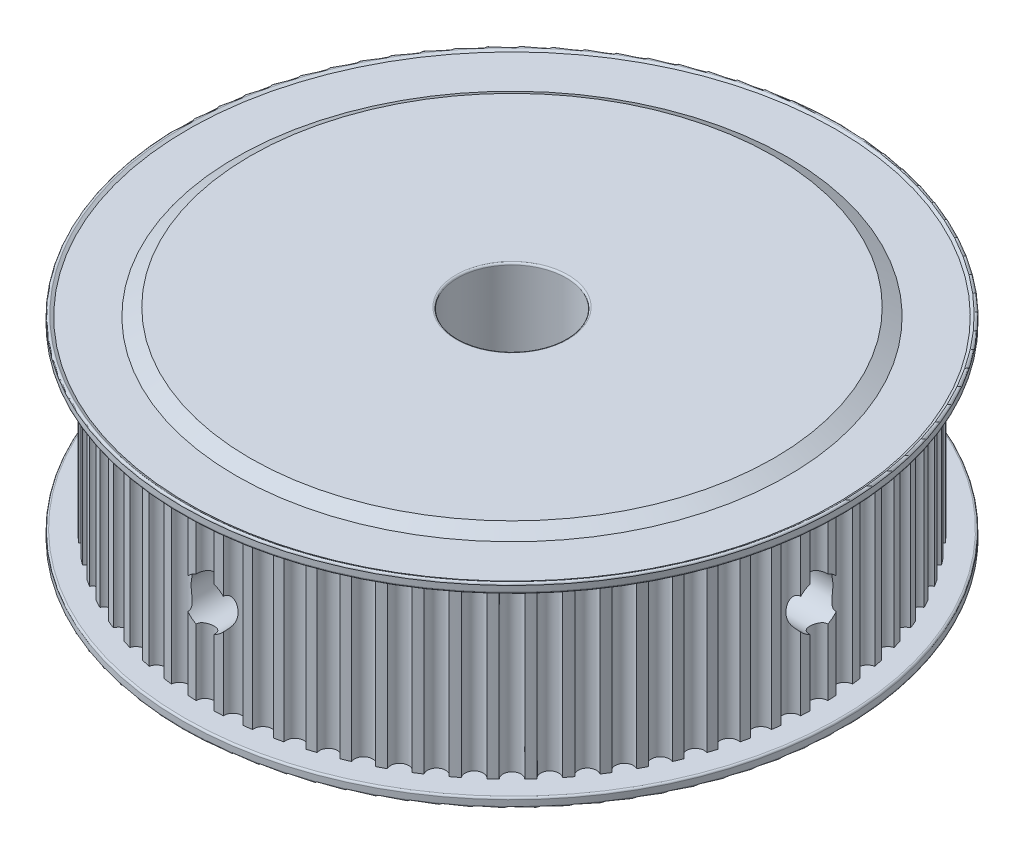
SolidWorks part; units mm, degrees
material "1060 Alloy"
ref_plane "Front Plane" through (0, 0, 0) normal (0, 0, 1) x (1, 0, 0)
ref_plane "Top Plane" through (0, 0, 0) normal (0, 1, 0) x (1, 0, 0)
ref_plane "Right Plane" through (0, 0, 0) normal (1, 0, 0) x (0, 0, -1)
sketch "Sketch1" plane through (0, 0, 0) normal (0, 0, 1) x (1, 0, 0)
  line L0 (0, 0) -> (0, 23) construction
  line L1 (0, 0) -> (0, 1.75)
  line L2 (0, 1.75) -> (36.5, 1.75)
  line L3 (36.5, 1.75) -> (36.5, 0.55)
  line L4 (36.5, 0.55) -> (35.8938, 0.9)
  line L5 (35.8938, 0.9) -> (30.5588, 0.9)
  line L6 (30.5588, 0.9) -> (29, 0)
  line L7 (29, 0) -> (0, 0)
  dimension "D1" = 23
  dimension "D3" = 36.5
  dimension "D4" = 29
  dimension "D5" = 150
  dimension "D6" = 150
  dimension "D7" = 1.75
  dimension "D8" = 1.2
  dimension "D9" = 0.85
revolve "Revolve1" add sketch "Sketch1" angle 360 about L0
fillet "Fillet1" radius 0.2 2 edges at (0, 0.55, -36.5) (0, 1.75, -36.5)
sketch "Sketch2" plane through (0, 1.75, 0) normal (0, 1, 0) x (1, 0, 0)
  arc A0 (1.9659, 33.9431) -> (0.9999, 33.9853) centre (0, 0) ccw
  circle A1 centre (0, 0) radius 33 construction
  arc A2 (-0.9999, 33.9853) -> (0.9999, 33.9853) centre (0, 34) ccw
  arc A3 (4.9168, 33.6426) -> (3.9581, 33.7688) centre (0, 0) ccw
  arc A4 (1.9659, 33.9431) -> (3.9581, 33.7688) centre (2.9633, 33.8706) ccw
  arc A5 (7.8302, 33.0861) -> (6.8862, 33.2954) centre (0, 0) ccw
  arc A6 (4.9168, 33.6426) -> (6.8862, 33.2954) centre (5.904, 33.4835) ccw
  arc A7 (10.6841, 32.2777) -> (9.7619, 32.5685) centre (0, 0) ccw
  arc A8 (7.8302, 33.0861) -> (9.7619, 32.5685) centre (8.7998, 32.8415) ccw
  arc A9 (13.4566, 31.2237) -> (12.5632, 31.5937) centre (0, 0) ccw
  arc A10 (10.6841, 32.2777) -> (12.5632, 31.5937) centre (11.6287, 31.9495) ccw
  arc A11 (16.1267, 29.9321) -> (15.269, 30.3786) centre (0, 0) ccw
  arc A12 (13.4566, 31.2237) -> (15.269, 30.3786) centre (14.369, 30.8145) ccw
  arc A13 (18.6741, 28.4126) -> (17.8586, 28.9322) centre (0, 0) ccw
  arc A14 (16.1267, 29.9321) -> (17.8586, 28.9322) centre (17, 29.4449) ccw
  arc A15 (21.0794, 26.677) -> (20.3122, 27.2656) centre (0, 0) ccw
  arc A16 (18.6741, 28.4126) -> (20.3122, 27.2656) centre (19.5016, 27.8512) ccw
  arc A17 (23.3242, 24.7383) -> (22.6113, 25.3915) centre (0, 0) ccw
  arc A18 (21.0794, 26.677) -> (22.6113, 25.3915) centre (21.8548, 26.0455) ccw
  arc A19 (25.3915, 22.6113) -> (24.7383, 23.3242) centre (0, 0) ccw
  arc A20 (23.3242, 24.7383) -> (24.7383, 23.3242) centre (24.0416, 24.0416) ccw
  arc A21 (27.2656, 20.3122) -> (26.677, 21.0794) centre (0, 0) ccw
  arc A22 (25.3915, 22.6113) -> (26.677, 21.0794) centre (26.0455, 21.8548) ccw
  arc A23 (28.9322, 17.8586) -> (28.4126, 18.6741) centre (0, 0) ccw
  arc A24 (27.2656, 20.3122) -> (28.4126, 18.6741) centre (27.8512, 19.5016) ccw
  arc A25 (30.3786, 15.269) -> (29.9321, 16.1267) centre (0, 0) ccw
  arc A26 (28.9322, 17.8586) -> (29.9321, 16.1267) centre (29.4449, 17) ccw
  arc A27 (31.5937, 12.5632) -> (31.2237, 13.4566) centre (0, 0) ccw
  arc A28 (30.3786, 15.269) -> (31.2237, 13.4566) centre (30.8145, 14.369) ccw
  arc A29 (32.5685, 9.7619) -> (32.2777, 10.6841) centre (0, 0) ccw
  arc A30 (31.5937, 12.5632) -> (32.2777, 10.6841) centre (31.9495, 11.6287) ccw
  arc A31 (33.2954, 6.8862) -> (33.0861, 7.8302) centre (0, 0) ccw
  arc A32 (32.5685, 9.7619) -> (33.0861, 7.8302) centre (32.8415, 8.7998) ccw
  arc A33 (33.7688, 3.9581) -> (33.6426, 4.9168) centre (0, 0) ccw
  arc A34 (33.2954, 6.8862) -> (33.6426, 4.9168) centre (33.4835, 5.904) ccw
  arc A35 (33.9853, 0.9999) -> (33.9431, 1.9659) centre (0, 0) ccw
  arc A36 (33.7688, 3.9581) -> (33.9431, 1.9659) centre (33.8706, 2.9633) ccw
  arc A37 (33.9431, -1.9659) -> (33.9853, -0.9999) centre (0, 0) ccw
  arc A38 (33.9853, 0.9999) -> (33.9853, -0.9999) centre (34, 0) ccw
  arc A39 (33.6426, -4.9168) -> (33.7688, -3.9581) centre (0, 0) ccw
  arc A40 (33.9431, -1.9659) -> (33.7688, -3.9581) centre (33.8706, -2.9633) ccw
  arc A41 (33.0861, -7.8302) -> (33.2954, -6.8862) centre (0, 0) ccw
  arc A42 (33.6426, -4.9168) -> (33.2954, -6.8862) centre (33.4835, -5.904) ccw
  arc A43 (32.2777, -10.6841) -> (32.5685, -9.7619) centre (0, 0) ccw
  arc A44 (33.0861, -7.8302) -> (32.5685, -9.7619) centre (32.8415, -8.7998) ccw
  arc A45 (31.2237, -13.4566) -> (31.5937, -12.5632) centre (0, 0) ccw
  arc A46 (32.2777, -10.6841) -> (31.5937, -12.5632) centre (31.9495, -11.6287) ccw
  arc A47 (29.9321, -16.1267) -> (30.3786, -15.269) centre (0, 0) ccw
  arc A48 (31.2237, -13.4566) -> (30.3786, -15.269) centre (30.8145, -14.369) ccw
  arc A49 (28.4126, -18.6741) -> (28.9322, -17.8586) centre (0, 0) ccw
  arc A50 (29.9321, -16.1267) -> (28.9322, -17.8586) centre (29.4449, -17) ccw
  arc A51 (26.677, -21.0794) -> (27.2656, -20.3122) centre (0, 0) ccw
  arc A52 (28.4126, -18.6741) -> (27.2656, -20.3122) centre (27.8512, -19.5016) ccw
  arc A53 (24.7383, -23.3242) -> (25.3915, -22.6113) centre (0, 0) ccw
  arc A54 (26.677, -21.0794) -> (25.3915, -22.6113) centre (26.0455, -21.8548) ccw
  arc A55 (22.6113, -25.3915) -> (23.3242, -24.7383) centre (0, 0) ccw
  arc A56 (24.7383, -23.3242) -> (23.3242, -24.7383) centre (24.0416, -24.0416) ccw
  arc A57 (20.3122, -27.2656) -> (21.0794, -26.677) centre (0, 0) ccw
  arc A58 (22.6113, -25.3915) -> (21.0794, -26.677) centre (21.8548, -26.0455) ccw
  arc A59 (17.8586, -28.9322) -> (18.6741, -28.4126) centre (0, 0) ccw
  arc A60 (20.3122, -27.2656) -> (18.6741, -28.4126) centre (19.5016, -27.8512) ccw
  arc A61 (15.269, -30.3786) -> (16.1267, -29.9321) centre (0, 0) ccw
  arc A62 (17.8586, -28.9322) -> (16.1267, -29.9321) centre (17, -29.4449) ccw
  arc A63 (12.5632, -31.5937) -> (13.4566, -31.2237) centre (0, 0) ccw
  arc A64 (15.269, -30.3786) -> (13.4566, -31.2237) centre (14.369, -30.8145) ccw
  arc A65 (9.7619, -32.5685) -> (10.6841, -32.2777) centre (0, 0) ccw
  arc A66 (12.5632, -31.5937) -> (10.6841, -32.2777) centre (11.6287, -31.9495) ccw
  arc A67 (6.8862, -33.2954) -> (7.8302, -33.0861) centre (0, 0) ccw
  arc A68 (9.7619, -32.5685) -> (7.8302, -33.0861) centre (8.7998, -32.8415) ccw
  arc A69 (3.9581, -33.7688) -> (4.9168, -33.6426) centre (0, 0) ccw
  arc A70 (6.8862, -33.2954) -> (4.9168, -33.6426) centre (5.904, -33.4835) ccw
  arc A71 (0.9999, -33.9853) -> (1.9659, -33.9431) centre (0, 0) ccw
  arc A72 (3.9581, -33.7688) -> (1.9659, -33.9431) centre (2.9633, -33.8706) ccw
  arc A73 (-1.9659, -33.9431) -> (-0.9999, -33.9853) centre (0, 0) ccw
  arc A74 (0.9999, -33.9853) -> (-0.9999, -33.9853) centre (0, -34) ccw
  arc A75 (-4.9168, -33.6426) -> (-3.9581, -33.7688) centre (0, 0) ccw
  arc A76 (-1.9659, -33.9431) -> (-3.9581, -33.7688) centre (-2.9633, -33.8706) ccw
  arc A77 (-7.8302, -33.0861) -> (-6.8862, -33.2954) centre (0, 0) ccw
  arc A78 (-4.9168, -33.6426) -> (-6.8862, -33.2954) centre (-5.904, -33.4835) ccw
  arc A79 (-10.6841, -32.2777) -> (-9.7619, -32.5685) centre (0, 0) ccw
  arc A80 (-7.8302, -33.0861) -> (-9.7619, -32.5685) centre (-8.7998, -32.8415) ccw
  arc A81 (-13.4566, -31.2237) -> (-12.5632, -31.5937) centre (0, 0) ccw
  arc A82 (-10.6841, -32.2777) -> (-12.5632, -31.5937) centre (-11.6287, -31.9495) ccw
  arc A83 (-16.1267, -29.9321) -> (-15.269, -30.3786) centre (0, 0) ccw
  arc A84 (-13.4566, -31.2237) -> (-15.269, -30.3786) centre (-14.369, -30.8145) ccw
  arc A85 (-18.6741, -28.4126) -> (-17.8586, -28.9322) centre (0, 0) ccw
  arc A86 (-16.1267, -29.9321) -> (-17.8586, -28.9322) centre (-17, -29.4449) ccw
  arc A87 (-21.0794, -26.677) -> (-20.3122, -27.2656) centre (0, 0) ccw
  arc A88 (-18.6741, -28.4126) -> (-20.3122, -27.2656) centre (-19.5016, -27.8512) ccw
  arc A89 (-23.3242, -24.7383) -> (-22.6113, -25.3915) centre (0, 0) ccw
  arc A90 (-21.0794, -26.677) -> (-22.6113, -25.3915) centre (-21.8548, -26.0455) ccw
  arc A91 (-25.3915, -22.6113) -> (-24.7383, -23.3242) centre (0, 0) ccw
  arc A92 (-23.3242, -24.7383) -> (-24.7383, -23.3242) centre (-24.0416, -24.0416) ccw
  arc A93 (-27.2656, -20.3122) -> (-26.677, -21.0794) centre (0, 0) ccw
  arc A94 (-25.3915, -22.6113) -> (-26.677, -21.0794) centre (-26.0455, -21.8548) ccw
  arc A95 (-28.9322, -17.8586) -> (-28.4126, -18.6741) centre (0, 0) ccw
  arc A96 (-27.2656, -20.3122) -> (-28.4126, -18.6741) centre (-27.8512, -19.5016) ccw
  arc A97 (-30.3786, -15.269) -> (-29.9321, -16.1267) centre (0, 0) ccw
  arc A98 (-28.9322, -17.8586) -> (-29.9321, -16.1267) centre (-29.4449, -17) ccw
  arc A99 (-31.5937, -12.5632) -> (-31.2237, -13.4566) centre (0, 0) ccw
  arc A100 (-30.3786, -15.269) -> (-31.2237, -13.4566) centre (-30.8145, -14.369) ccw
  arc A101 (-32.5685, -9.7619) -> (-32.2777, -10.6841) centre (0, 0) ccw
  arc A102 (-31.5937, -12.5632) -> (-32.2777, -10.6841) centre (-31.9495, -11.6287) ccw
  arc A103 (-33.2954, -6.8862) -> (-33.0861, -7.8302) centre (0, 0) ccw
  arc A104 (-32.5685, -9.7619) -> (-33.0861, -7.8302) centre (-32.8415, -8.7998) ccw
  arc A105 (-33.7688, -3.9581) -> (-33.6426, -4.9168) centre (0, 0) ccw
  arc A106 (-33.2954, -6.8862) -> (-33.6426, -4.9168) centre (-33.4835, -5.904) ccw
  arc A107 (-33.9853, -0.9999) -> (-33.9431, -1.9659) centre (0, 0) ccw
  arc A108 (-33.7688, -3.9581) -> (-33.9431, -1.9659) centre (-33.8706, -2.9633) ccw
  arc A109 (-33.9431, 1.9659) -> (-33.9853, 0.9999) centre (0, 0) ccw
  arc A110 (-33.9853, -0.9999) -> (-33.9853, 0.9999) centre (-34, 0) ccw
  arc A111 (-33.6426, 4.9168) -> (-33.7688, 3.9581) centre (0, 0) ccw
  arc A112 (-33.9431, 1.9659) -> (-33.7688, 3.9581) centre (-33.8706, 2.9633) ccw
  arc A113 (-33.0861, 7.8302) -> (-33.2954, 6.8862) centre (0, 0) ccw
  arc A114 (-33.6426, 4.9168) -> (-33.2954, 6.8862) centre (-33.4835, 5.904) ccw
  arc A115 (-32.2777, 10.6841) -> (-32.5685, 9.7619) centre (0, 0) ccw
  arc A116 (-33.0861, 7.8302) -> (-32.5685, 9.7619) centre (-32.8415, 8.7998) ccw
  arc A117 (-31.2237, 13.4566) -> (-31.5937, 12.5632) centre (0, 0) ccw
  arc A118 (-32.2777, 10.6841) -> (-31.5937, 12.5632) centre (-31.9495, 11.6287) ccw
  arc A119 (-29.9321, 16.1267) -> (-30.3786, 15.269) centre (0, 0) ccw
  arc A120 (-31.2237, 13.4566) -> (-30.3786, 15.269) centre (-30.8145, 14.369) ccw
  arc A121 (-28.4126, 18.6741) -> (-28.9322, 17.8586) centre (0, 0) ccw
  arc A122 (-29.9321, 16.1267) -> (-28.9322, 17.8586) centre (-29.4449, 17) ccw
  arc A123 (-26.677, 21.0794) -> (-27.2656, 20.3122) centre (0, 0) ccw
  arc A124 (-28.4126, 18.6741) -> (-27.2656, 20.3122) centre (-27.8512, 19.5016) ccw
  arc A125 (-24.7383, 23.3242) -> (-25.3915, 22.6113) centre (0, 0) ccw
  arc A126 (-26.677, 21.0794) -> (-25.3915, 22.6113) centre (-26.0455, 21.8548) ccw
  arc A127 (-22.6113, 25.3915) -> (-23.3242, 24.7383) centre (0, 0) ccw
  arc A128 (-24.7383, 23.3242) -> (-23.3242, 24.7383) centre (-24.0416, 24.0416) ccw
  arc A129 (-20.3122, 27.2656) -> (-21.0794, 26.677) centre (0, 0) ccw
  arc A130 (-22.6113, 25.3915) -> (-21.0794, 26.677) centre (-21.8548, 26.0455) ccw
  arc A131 (-17.8586, 28.9322) -> (-18.6741, 28.4126) centre (0, 0) ccw
  arc A132 (-20.3122, 27.2656) -> (-18.6741, 28.4126) centre (-19.5016, 27.8512) ccw
  arc A133 (-15.269, 30.3786) -> (-16.1267, 29.9321) centre (0, 0) ccw
  arc A134 (-17.8586, 28.9322) -> (-16.1267, 29.9321) centre (-17, 29.4449) ccw
  arc A135 (-12.5632, 31.5937) -> (-13.4566, 31.2237) centre (0, 0) ccw
  arc A136 (-15.269, 30.3786) -> (-13.4566, 31.2237) centre (-14.369, 30.8145) ccw
  arc A137 (-9.7619, 32.5685) -> (-10.6841, 32.2777) centre (0, 0) ccw
  arc A138 (-12.5632, 31.5937) -> (-10.6841, 32.2777) centre (-11.6287, 31.9495) ccw
  arc A139 (-6.8862, 33.2954) -> (-7.8302, 33.0861) centre (0, 0) ccw
  arc A140 (-9.7619, 32.5685) -> (-7.8302, 33.0861) centre (-8.7998, 32.8415) ccw
  arc A141 (-3.9581, 33.7688) -> (-4.9168, 33.6426) centre (0, 0) ccw
  arc A142 (-6.8862, 33.2954) -> (-4.9168, 33.6426) centre (-5.904, 33.4835) ccw
  arc A143 (-0.9999, 33.9853) -> (-1.9659, 33.9431) centre (0, 0) ccw
  arc A144 (-3.9581, 33.7688) -> (-1.9659, 33.9431) centre (-2.9633, 33.8706) ccw
  dimension "D1" = 68
  dimension "D2" = 66
  dimension "D3" = 72
extrude "Boss-Extrude1" add sketch "Sketch2" along normal blind 19.5
ref_plane "Plane1" through (0, 11.5, 0) normal (0, 1, 0) x (1, 0, 0)
mirror "Mirror1" about plane through (0, 11.5, 0) normal (0, 1, 0) of "Fillet1", "Revolve1"
sketch "Sketch4" plane through (0, 0, 0) normal (0, 0, 1) x (1, 0, 0)
  line L0 (-0.9999, 21.25) -> (-0.9999, 1.75) construction
  circle A0 centre (0, 11.5) radius 2.6
  point P5 (-0.9999, 11.5)
  dimension "D1" = 5.2
extrude "Cut-Extrude1" cut sketch "Sketch4" along normal blind 36.5
sketch "Sketch5" plane through (0, 0, 0) normal (1, 0, 0) x (0, 0, -1)
  line L1 (-0.9999, 21.25) -> (-0.9999, 1.75) construction
  circle A0 centre (0, 11.5) radius 2.6
  point P5 (-0.9999, 11.5)
  dimension "D1" = 5.2
extrude "Cut-Extrude2" cut sketch "Sketch5" along normal blind 36.5
sketch "Sketch3" plane through (0, 23, 0) normal (0, 1, 0) x (1, 0, 0)
  circle A0 centre (0, 0) radius 6
  dimension "D1" = 12
extrude "Cut-Extrude3" cut sketch "Sketch3" against normal through all
fillet "Fillet2" radius 0.2 2 edges at (0, 0, 6) (0, 23, 6)
scale "Scale2" scale about centroid uniform scaling yes scale factor 0.2
